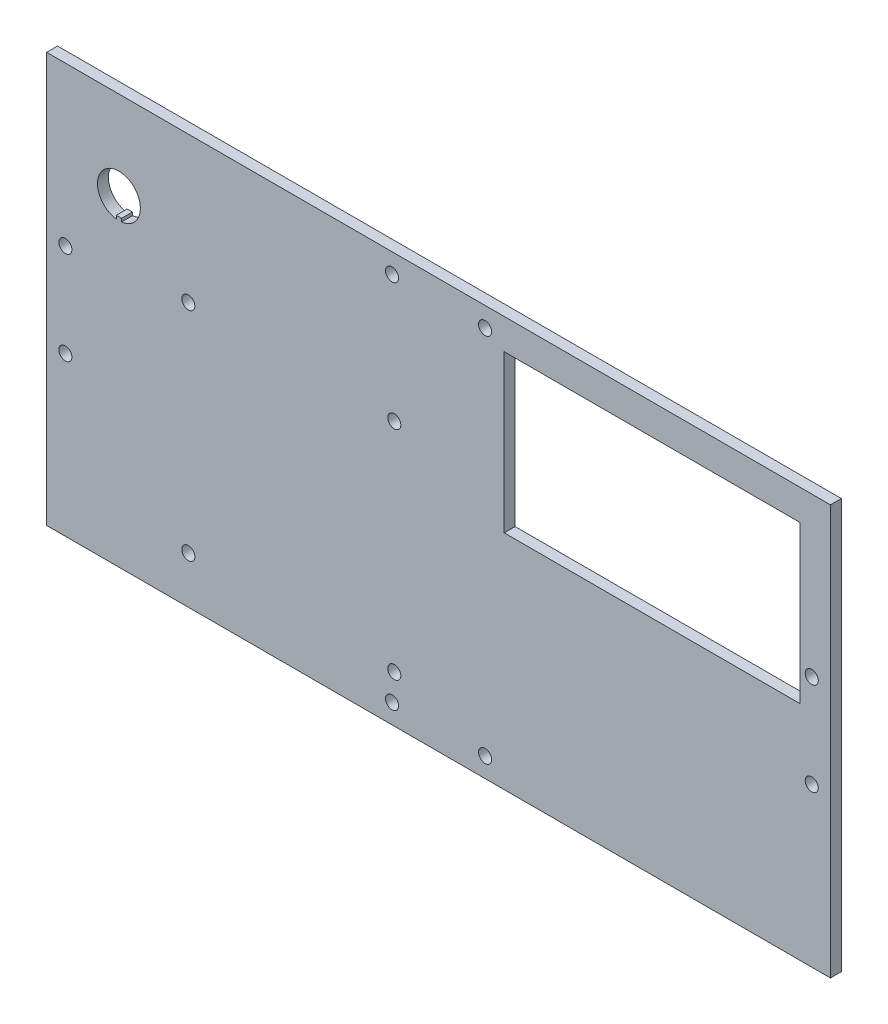
SolidWorks part; units mm, degrees
material "6061-T6 (SS)"
ref_plane "Front Plane" through (0, 0, 0) normal (0, 0, 1) x (1, 0, 0)
ref_plane "Top Plane" through (0, 0, 0) normal (0, 1, 0) x (1, 0, 0)
ref_plane "Right Plane" through (0, 0, 0) normal (1, 0, 0) x (0, 0, -1)
sketch "Sketch1" plane through (0, 0, 0) normal (0, 0, 1) x (1, 0, 0)
  line L0 (-108.7209, 13.5509) -> (-108.7209, -13.5509) construction
  line L1 (-114.173, -59.69) -> (114.173, -59.69)
  line L2 (-114.173, -59.69) -> (-114.173, 59.69)
  line L3 (-114.173, 59.69) -> (114.173, 59.69)
  line L4 (114.173, -59.69) -> (114.173, 59.69)
  line L5 (-114.173, -59.69) -> (114.173, 59.69) construction
  line L6 (-114.173, 59.69) -> (114.173, -59.69) construction
  line L7 (-108.7209, 0) -> (-114.173, 0) construction
  line L8 (0, 0) -> (0, 59.69) construction
  line L9 (-93.8779, 27.7812) -> (-93.8779, 28.7251)
  line L10 (19.133, 50.8) -> (105.283, 50.8)
  line L11 (19.133, 50.8) -> (19.133, 5.1)
  line L12 (19.133, 5.1) -> (105.283, 5.1)
  line L13 (105.283, 50.8) -> (105.283, 5.1)
  line L14 (-93.8779, 28.7251) -> (-92.3539, 28.7251)
  line L15 (-92.3539, 28.7251) -> (-92.3539, 27.7812)
  line L16 (-93.1159, 28.7251) -> (-93.1159, 40.2313) construction
  line L17 (-56.515, 38.7691) -> (-56.515, 29.1968) construction
  line L18 (-29.591, 38.7691) -> (-29.591, 29.1968) construction
  line L19 (-43.053, -39.7921) -> (-43.053, 11.0079) construction
  line L20 (-101.473, 11.0079) -> (15.367, 11.0079) construction
  line L21 (-101.473, 11.0079) -> (-101.473, -39.7921) construction
  line L22 (-101.473, -39.7921) -> (15.367, -39.7921) construction
  line L23 (15.367, 11.0079) -> (15.367, -39.7921) construction
  line L24 (-18.923, -39.7921) -> (-7.493, -39.7921) construction
  line L25 (-18.923, -39.7921) -> (-18.923, -51.2221) construction
  line L26 (-18.923, -51.2221) -> (-7.493, -51.2221) construction
  line L27 (-7.493, -39.7921) -> (-7.493, -51.2221) construction
  line L28 (-18.923, 11.0079) -> (-7.493, 11.0079) construction
  line L29 (-18.923, 11.0079) -> (-18.923, 22.4379) construction
  line L30 (-18.923, 22.4379) -> (-7.493, 22.4379) construction
  line L31 (-7.493, 11.0079) -> (-7.493, 22.4379) construction
  line L32 (-78.613, -39.7921) -> (-78.613, -51.2221) construction
  line L33 (-67.183, -51.2221) -> (-78.613, -51.2221) construction
  line L34 (-67.183, -39.7921) -> (-67.183, -51.2221) construction
  line L35 (-67.183, -39.7921) -> (-78.613, -39.7921) construction
  line L36 (-78.613, 11.0079) -> (-78.613, 22.4379) construction
  line L37 (-67.183, 22.4379) -> (-78.613, 22.4379) construction
  line L38 (-67.183, 11.0079) -> (-67.183, 22.4379) construction
  line L39 (-67.183, 11.0079) -> (-78.613, 11.0079) construction
  line L40 (-72.898, -51.2221) -> (-72.898, -46.0171) construction
  line L41 (-72.898, -46.0171) -> (-12.898, -46.0171) construction
  line L42 (-72.898, -46.0171) -> (-72.898, 17.2329) construction
  line L43 (-72.898, 17.2329) -> (-12.898, 17.2329) construction
  line L44 (-12.898, -46.0171) -> (-12.898, 17.2329) construction
  line L45 (-101.473, -14.3921) -> (-72.898, -14.3921) construction
  line L46 (-13.5509, 53.975) -> (13.5509, 53.975) construction
  line L47 (0, 53.975) -> (0, 59.69) construction
  circle A0 centre (-108.7209, 13.5509) radius 1.905
  circle A1 centre (-108.7209, -13.5509) radius 1.905
  circle A2 centre (108.7209, -13.5509) radius 1.905
  circle A3 centre (108.7209, 13.5509) radius 1.905
  circle A4 centre (-43.053, 33.9829) radius 14.2875 construction
  circle A5 centre (-93.1159, 33.9829) radius 6.2484
  circle A6 centre (-12.898, 17.2329) radius 1.905
  circle A7 centre (-12.898, -46.0171) radius 1.905
  circle A8 centre (-72.898, -46.0171) radius 1.905
  circle A9 centre (-72.898, 17.2329) radius 1.905
  circle A10 centre (-13.5509, 53.975) radius 1.905
  circle A11 centre (13.5509, 53.975) radius 1.905
  circle A12 centre (13.5509, -53.975) radius 1.905
  circle A13 centre (-13.5509, -53.975) radius 1.905
  point P0 (0, 0)
  point P34 (-56.515, 33.9829)
  dimension "D3" = 3.81
  dimension "D6" = 28.575
  dimension "D9" = 12.4968
  dimension "D25" = 3.81
  dimension "D1" = 228.346
  dimension "D2" = 119.38
  dimension "D4" = 108.7209
  dimension "D5" = 27.1018
  dimension "D7" = 86.15
  dimension "D8" = 45.7
  dimension "D10" = 1.524
  dimension "D11" = 11.5062
  dimension "D12" = 26.924
  dimension "D13" = 13.462
  dimension "D14" = 50.8
  dimension "D15" = 116.84
  dimension "D16" = 73.66
  dimension "D17" = 22.86
  dimension "D18" = 11.43
  dimension "D22" = 8.89
  dimension "D23" = 12.7
  dimension "D26" = 63.25
  dimension "D27" = 60
  dimension "D28" = 5.715
  dimension "D29" = 8.89
extrude "Boss-Extrude1" add sketch "Sketch1" along normal blind 3.175 contours L1 L4 L3 L2 A12 A11 A10 A9 A8 A7 A6 A5 A4 A2 A1 A0 L10 L13 L12 L11 A3 A13 | L9 A5 L15 L14 | L17 A4 | L18 A4
sketch "Sketch2" plane through (0, 0, 3.175) normal (0, 0, 1) x (1, 0, 0)
  line L0 (79.273, -24.83) -> (98.273, -48.83) construction
  circle A0 centre (88.773, -36.83) radius 12
  circle A1 centre (79.273, -24.83) radius 1.55
  circle A2 centre (98.273, -48.83) radius 1.55
  point P7 (88.773, -36.83)
  dimension "D3" = 3.1
  dimension "D4" = 24
  dimension "D1" = 19
  dimension "D2" = 24
  dimension "D5" = 25.4
  dimension "D6" = 22.86
extrude "Cut-Extrude1" [suppressed] cut sketch "Sketch2" against normal through all
sketch "Sketch3" plane through (0, 0, 3.175) normal (0, 0, 1) x (1, 0, 0)
  line L0 (-29.591, 38.7691) -> (-29.591, 29.1968) construction
  line L1 (-56.515, 38.7691) -> (-56.515, 29.1968) construction
  line L2 (-29.591, 38.7691) -> (-29.591, 29.1968)
  line L3 (-56.515, 38.7691) -> (-56.515, 29.1968)
  circle A0 centre (-43.053, 33.9829) radius 14.2875 construction
  circle A1 centre (-43.053, 33.9829) radius 14.2875
extrude "Cut-Extrude2" [suppressed] cut sketch "Sketch3" against normal through all contours L2 A1 L3
